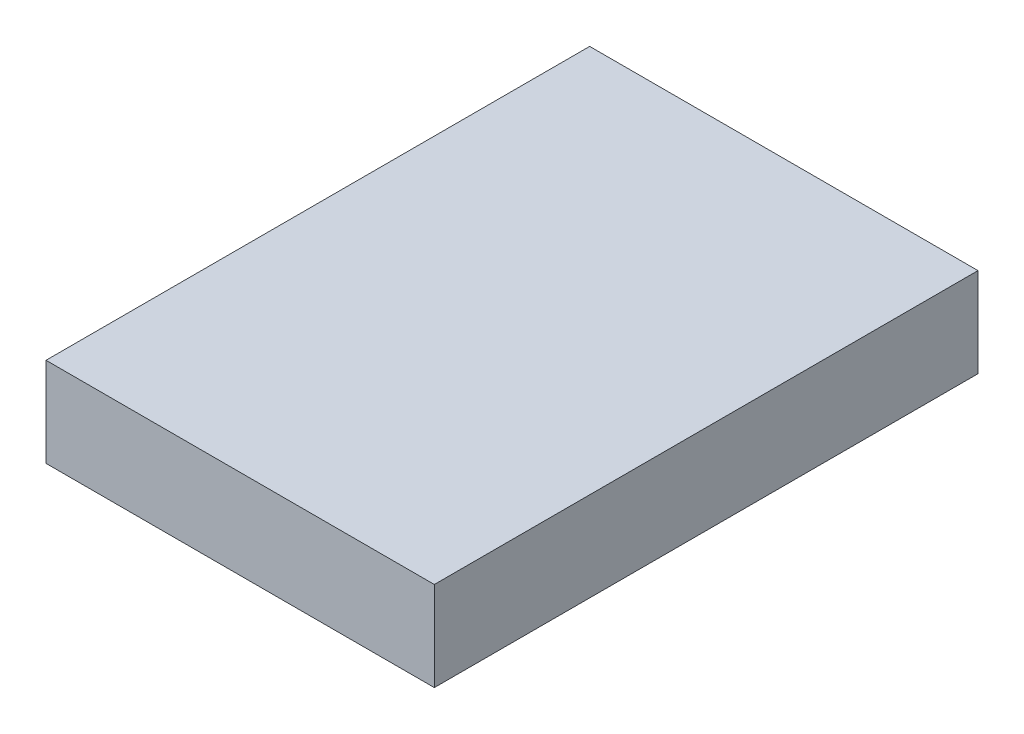
SolidWorks part; units mm, degrees
ref_plane "Front Plane" through (0, 0, 0) normal (0, 0, 1) x (1, 0, 0)
ref_plane "Top Plane" through (0, 0, 0) normal (0, 1, 0) x (1, 0, 0)
ref_plane "Right Plane" through (0, 0, 0) normal (1, 0, 0) x (0, 0, -1)
sketch "Sketch1" plane through (0, 0, 0) normal (0, 1, 0) x (1, 0, 0)
  line L1 (-2.0876, 18.8531) -> (22.9124, 18.8531)
  line L2 (-2.0876, 18.8531) -> (-2.0876, -16.1469)
  line L3 (-2.0876, -16.1469) -> (22.9124, -16.1469)
  line L4 (22.9124, 18.8531) -> (22.9124, -16.1469)
  dimension "D1" = 35
  dimension "D2" = 25
extrude "Boss-Extrude1" add sketch "Sketch1" along normal blind 5.75
